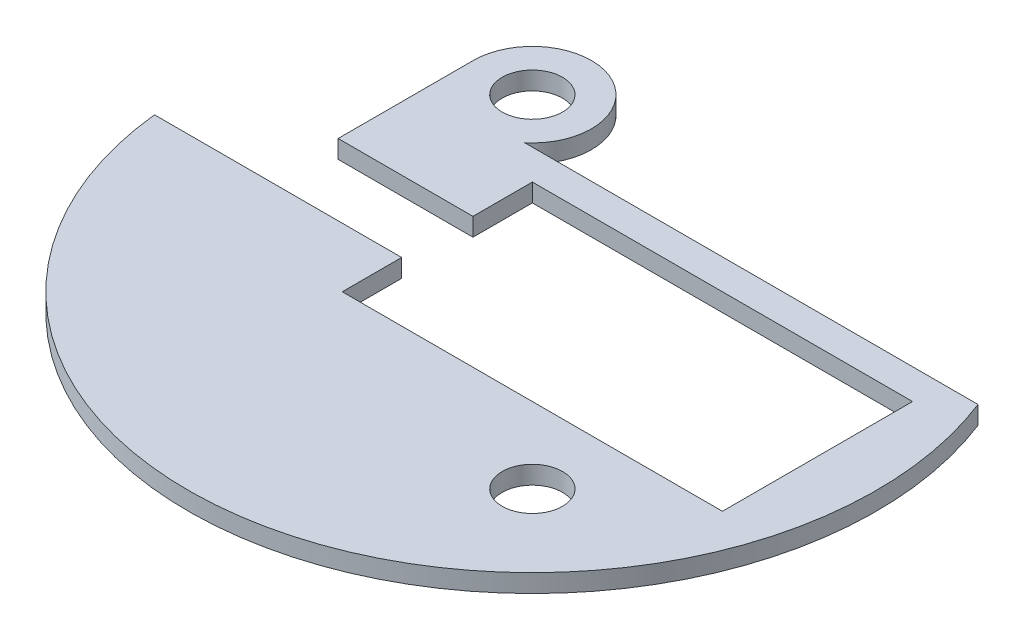
SolidWorks part; units mm, degrees
ref_plane "Front Plane" through (0, 0, 0) normal (0, 0, 1) x (1, 0, 0)
ref_plane "Top Plane" through (0, 0, 0) normal (0, 1, 0) x (1, 0, 0)
ref_plane "Right Plane" through (0, 0, 0) normal (1, 0, 0) x (0, 0, -1)
sketch "Sketch2" plane through (0, 0, 0) normal (0, 1, 0) x (1, 0, 0)
  line L0 (-24.1835, 17.9605) -> (-24.1835, 3.75)
  line L1 (-17.9605, 17.9605) -> (17.9605, 17.9605) construction
  line L2 (-17.9605, 17.9605) -> (-17.9605, -17.9605) construction
  line L3 (-17.9605, -17.9605) -> (17.9605, -17.9605) construction
  line L4 (17.9605, 17.9605) -> (17.9605, -17.9605) construction
  line L5 (-17.9605, 17.9605) -> (17.9605, -17.9605) construction
  line L6 (-17.9605, -17.9605) -> (17.9605, 17.9605) construction
  line L7 (30, -10) -> (11.7375, -10)
  line L8 (30, -10) -> (30, 10)
  line L9 (30, 10) -> (-10, 10)
  line L10 (-10, -10) -> (-10, -3.75)
  line L11 (30, -10) -> (-10, 10) construction
  line L12 (30, 10) -> (-10, -10) construction
  line L13 (-24.1835, -3.75) -> (-10, -3.75)
  line L14 (-24.1835, -3.75) -> (-24.1835, 3.75) construction
  line L15 (-24.1835, 3.75) -> (-10, 3.75)
  line L16 (-10, 0) -> (-10, 3.75) construction
  line L17 (-24.1835, -3.75) -> (-10, 3.75) construction
  line L18 (-24.1835, 3.75) -> (-10, -3.75) construction
  line L19 (11.7375, -25.875) -> (-23.8225, -25.875) construction
  line L20 (11.7375, -11.7375) -> (11.7375, -10) construction
  line L21 (-17.9605, -10) -> (-23.8225, -10) construction
  line L22 (-23.8225, -25.875) -> (-23.8225, -10) construction
  line L23 (11.7375, -25.875) -> (-23.8225, -10) construction
  line L24 (11.7375, -10) -> (-23.8225, -25.875) construction
  line L25 (-24.1835, -3.75) -> (-36.0002, -3.75)
  line L28 (-10, -3.75) -> (-10, 0) construction
  line L29 (-10, 3.75) -> (-10, 10)
  line L30 (-10, -3.75) -> (-10, 0) construction
  line L31 (-10, 0) -> (-10, 3.75) construction
  line L32 (11.7375, -10) -> (10, -10)
  line L33 (0, -10) -> (-10, -10)
  line L34 (11.7375, -10) -> (10, -10) construction
  line L35 (10, -10) -> (0, -10)
  line L36 (10, -10) -> (0, -10) construction
  line L37 (0, -10) -> (-10, -10) construction
  line L38 (11.7375, -25.875) -> (11.7375, -17.9605) construction
  line L39 (11.7375, -17.9605) -> (11.7375, -11.7375) construction
  line L40 (-10, -10) -> (-17.9605, -10) construction
  line L41 (33.712, 13.175) -> (-13.9825, 13.175)
  line L42 (-10.833, 29.691) -> (25.997, 29.691) construction
  line L43 (-10.833, 29.691) -> (-10.833, 13.1678) construction
  line L44 (-10.833, 13.1678) -> (25.997, 13.1678) construction
  line L45 (25.997, 29.691) -> (25.997, 13.1678) construction
  line L46 (-10.833, 29.691) -> (25.997, 13.1678) construction
  line L47 (-10.833, 13.1678) -> (25.997, 29.691) construction
  circle A0 centre (0, 0) radius 10 construction
  circle A1 centre (-17.9605, 17.9605) radius 3.175
  circle A2 centre (17.9605, 17.9605) radius 3.175 construction
  circle A3 centre (17.9605, -17.9605) radius 3.175
  circle A4 centre (-17.9605, -17.9605) radius 3.175 construction
  arc A5 (-36.0002, -3.75) -> (33.712, 13.175) centre (0, 0) ccw
  arc A6 (13.5602, -13.5602) -> (11.7375, -17.9605) centre (17.9605, -17.9605) ccw construction
  arc A7 (-17.9605, 24.1835) -> (-24.1835, 17.9605) centre (-17.9605, 17.9605) ccw
  arc A8 (24.1835, 17.9605) -> (17.9605, 24.1835) centre (17.9605, 17.9605) ccw construction
  arc A9 (33.712, 13.175) -> (-36.0002, -3.75) centre (0, 0) ccw construction
  arc A10 (11.7375, 17.9605) -> (13.5602, 13.5602) centre (17.9605, 17.9605) ccw construction
  arc A11 (17.9605, 24.1835) -> (11.7375, 17.9605) centre (17.9605, 17.9605) ccw construction
  arc A12 (13.5602, 13.5602) -> (17.9605, 11.7375) centre (17.9605, 17.9605) ccw construction
  arc A13 (17.9605, 11.7375) -> (24.1835, 17.9605) centre (17.9605, 17.9605) ccw construction
  arc A14 (-24.1835, 17.9605) -> (-17.9605, 11.7375) centre (-17.9605, 17.9605) ccw construction
  arc A15 (-17.9605, 11.7375) -> (-13.5602, 13.5602) centre (-17.9605, 17.9605) ccw construction
  arc A16 (-13.9825, 13.175) -> (-11.7375, 17.9605) centre (-17.9605, 17.9605) ccw
  arc A17 (-11.7375, 17.9605) -> (-17.9605, 24.1835) centre (-17.9605, 17.9605) ccw
  arc A18 (11.7375, -17.9605) -> (17.9605, -11.7375) centre (17.9605, -17.9605) ccw construction
  arc A19 (17.9605, -11.7375) -> (13.5602, -13.5602) centre (17.9605, -17.9605) ccw construction
  arc A20 (-13.5602, 13.5602) -> (-13.9825, 13.175) centre (-17.9605, 17.9605) ccw construction
  point P11 (10, 0)
  point P17 (-17.0918, 0)
  point P23 (-6.0425, -17.9375)
  point P46 (7.582, 21.4294)
  point P51 (7.582, 21.4294)
  point P58 (57.2898, 40.2093)
  point P59 (0, 0)
  point P60 (54.8226, -56.7862)
  dimension "D1" = 6.35
  dimension "D3" = 20
  dimension "D5" = 72.39
  dimension "D2" = 50.8
  dimension "D4" = 40
  dimension "D6" = 7.5
  dimension "D7" = 35.56
  dimension "D8" = 15.875
  dimension "D9" = 3.048
  dimension "D10" = 36.83
  dimension "D11" = 16.5232
  dimension "D12" = 3.175
extrude "Boss-Extrude1" add sketch "Sketch2" along normal blind 1.905
equation "\"AIRFRAME_OD\"= 3.142in"
equation "\"AIRFRAME_ID\"= 3.00in"
equation "\"FLAT_T\"= 0.125in"
equation "\"NOSE_EXP_L\"= 3.5in"
equation "\"NOSE_SHOULDER_L\"= 1.5in"
equation "\"MAIN_L\"= 30in"
equation "\"RECO_COUP_L\"= 6in"
equation "\"RECO_SWITCH_L\"= 1.5in"
equation "\"DROGUE_L\"= 14in"
equation "\"ATS_FORE_COUP_L\"= 4in"
equation "\"ATS_AFT_COUP_L\"= 2.5in"
equation "\"LOWER_L\"= 16in"
equation "\"FIN_N\"= 4"
equation "\"CR_AFT_X\"= 0.5in"
equation "\"CR_FORE_X\"= 6in"
equation "\"COUPLER_OD\"= 2.998in"
equation "\"COUPLER_ID\"= 2.875in"
equation "\"RECO_ROD_X\"= 1.5in"
equation "\"ATS_ROD_X\"= 2in"
equation "\"FIN_ROOT\"= 5in"
equation "\"FIN_X\"= 0.75in"
equation "\"MOTOR_OD\"= 2.25in"
equation "\"MOTOR_ID\"= 2.126in"
equation "\"MOTOR_L\"= 8in"
equation "\"MOTOR_LOWER_X\"= 0.5in"
equation "\"NOSE_CONE_L\"=14.5in"
equation "\"ATS_LIPO_L\" = 2.8in"
equation "\"ATS_LIPO_W\" = 0.625in"
equation "\"ATS_LIPO_H\" = 1.4in "
equation "\"ATS_STANDOFF_H\" = 10mm"
equation "\"ATS_STANDOFF_OD\" = 5.2mm"
equation "\"ATS_PCB_L\" = 2.5in"
equation "\"ATS_PCB_W\" = 1.45in"
equation "\"ATS_PCB_H\" = 1.2in"
equation "\"ATS_PCB_HOLESEP_W\" = 1.33in - 0.0985in"
equation "\"ATS_ALTI_L\" = 1.05in"
equation "\"ATS_ALTI_W\" = 0.7in"
equation "\"ATS_ALTI_H\" = 0.4in"
equation "\"D7@Sketch2\"=\"ATS_LIPO_H\""
equation "\"D8@Sketch2\"=\"ATS_LIPO_W\""
equation "\"D10@Sketch2\"=\"ATS_PCB_W\""
